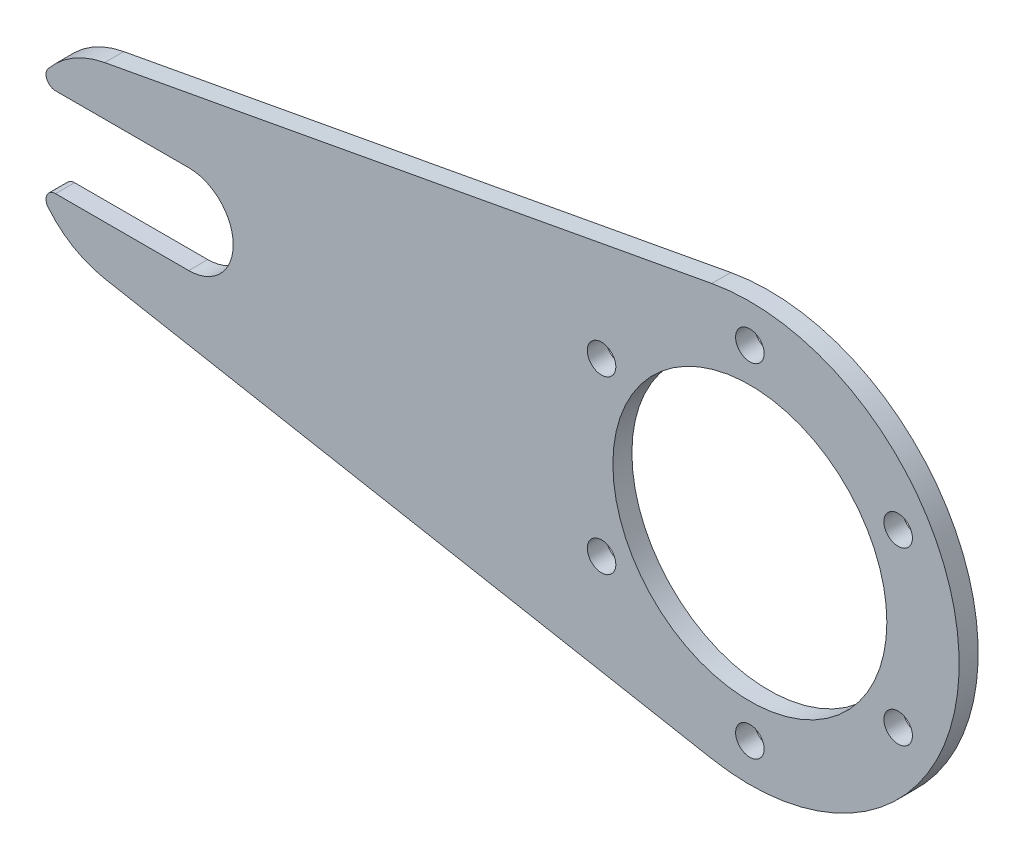
SolidWorks part; units mm, degrees
ref_plane "Front Plane" through (0, 0, 0) normal (0, 0, 1) x (1, 0, 0)
ref_plane "Top Plane" through (0, 0, 0) normal (0, 1, 0) x (1, 0, 0)
ref_plane "Right Plane" through (0, 0, 0) normal (1, 0, 0) x (0, 0, -1)
sketch "Sketch1" plane through (0, 0, 0) normal (0, 0, 1) x (1, 0, 0)
  line L0 (-215.3227, 31.2208) -> (-12.7, 68.6858)
  line L1 (-215.3227, -31.2208) -> (-12.7, -68.6858)
  line L2 (-209.55, 0) -> (0, 0) construction
  line L6 (-231.7154, 14.859) -> (-187.2654, 14.859)
  line L7 (-231.7154, -14.859) -> (-187.2654, -14.859)
  arc A0 (-12.7, -68.6858) -> (-12.7, 68.6858) centre (0, 0) ccw
  arc A1 (-215.3227, 31.2208) -> (-234.1782, 20.0378) centre (-209.55, 0) ccw
  circle A2 centre (0, 0) radius 57.15 construction
  circle A3 centre (0, 57.15) radius 4.7625
  circle A4 centre (49.4934, 28.575) radius 4.7625
  circle A5 centre (49.4934, -28.575) radius 4.7625
  circle A6 centre (0, -57.15) radius 4.7625
  circle A7 centre (-49.4934, -28.575) radius 4.7625
  circle A8 centre (-49.4934, 28.575) radius 4.7625
  arc A9 (-234.1782, -20.0378) -> (-231.7154, -14.859) centre (-231.7154, -18.034) cw
  circle A10 centre (0, 0) radius 45.72
  arc A12 (-187.2654, -14.859) -> (-187.2654, 14.859) centre (-187.2654, 0) ccw
  arc A13 (-234.1782, -20.0378) -> (-215.3227, -31.2208) centre (-209.55, 0) ccw
  arc A14 (-234.1782, 20.0378) -> (-231.7154, 14.859) centre (-231.7154, 18.034) ccw
  point P22 (0, 0)
  point P24 (-196.3099, 31.1047)
  point P25 (-14.0111, 68.4303)
  point P27 (-12.1005, -59.0989)
  point P28 (-196.3099, -31.1047)
  point P30 (-189.9412, 0)
  point P32 (-139.1412, 0)
  point P39 (71.12, 0)
  dimension "D1" = 139.7
  dimension "D2" = 63.5
  dimension "D4" = 114.3
  dimension "D5" = 9.525
  dimension "D6" = 6
  dimension "D7" = 91.44
  dimension "D8" = 14.859
  dimension "D10" = 44.45
  dimension "D9" = 3.175
  dimension "D3" = 209.55
extrude "Boss-Extrude1" add sketch "Sketch1" along normal blind 6.35
ref_plane "Plane1" through (0, 0, 25.4) normal (0, 0, 1) x (1, 0, 0)
sketch "Sketch3" plane through (0, 0, 25.4) normal (0, 0, 1) x (1, 0, 0)
  text T0 "V M S" font "Magneto" height in points 68
wrap "Wrap1" [suppressed] sketch "Sketch3" source sketch "Sketch3" thickness 6.35 parameters "D1"=6.35
fillet "Fillet2" [suppressed] radius 0.7937
sketch "Sketch4" plane through (0, 0, 0) normal (0, 0, -1) x (-1, 0, 0)
  line L0 (0, 0) -> (165.1264, 0) construction
  line L1 (234.95, -82.55) -> (-69.85, -82.55)
  line L2 (234.95, -82.55) -> (234.95, 82.55)
  line L3 (234.95, 82.55) -> (-69.85, 82.55)
  line L4 (-69.85, -82.55) -> (-69.85, 82.55)
  line L5 (234.95, -82.55) -> (-69.85, 82.55) construction
  line L6 (234.95, 82.55) -> (-69.85, -82.55) construction
  arc A0 (12.7, 68.6858) -> (12.7, -68.6858) centre (0, 0) ccw construction
  point P0 (82.55, 0)
  dimension "D1" = 304.8
  dimension "D2" = 165.1
